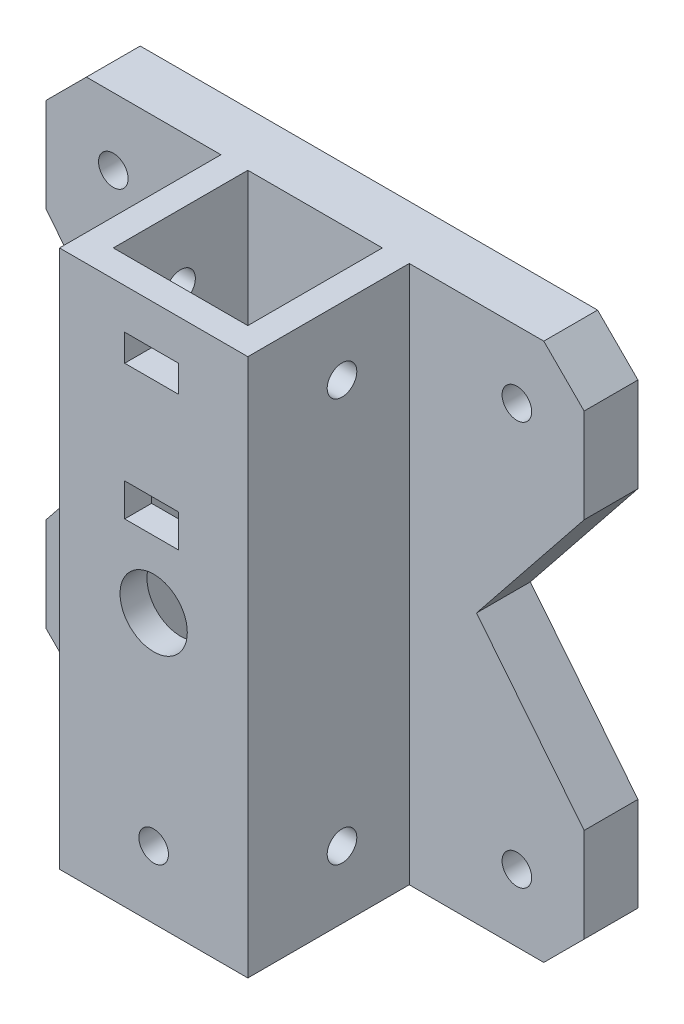
SolidWorks part; units mm, degrees
ref_plane "Plan de face" through (0, 0, 0) normal (0, 0, 1) x (1, 0, 0)
ref_plane "Plan de dessus" through (0, 0, 0) normal (0, 1, 0) x (1, 0, 0)
ref_plane "Plan de droite" through (0, 0, 0) normal (1, 0, 0) x (0, 0, -1)
sketch "Esquisse1" plane through (0, 0, 0) normal (0, 0, 1) x (1, 0, 0)
  line L1 (-40, 40) -> (40, 40)
  line L2 (-40, 40) -> (-40, -40)
  line L3 (-40, -40) -> (40, -40)
  line L4 (40, 40) -> (40, -40)
  line L5 (-40, 40) -> (40, -40) construction
  line L6 (-40, -40) -> (40, 40) construction
  point P0 (0, 0)
  dimension "D1" = 80
  dimension "D2" = 80
extrude "Boss.-Extru.1" add sketch "Esquisse1" along normal blind 8
sketch "Esquisse2" plane through (0, 40, 0) normal (0, 1, 0) x (1, 0, 0)
  line L0 (40, -8) -> (-40, -8) construction
  line L1 (-10, -8) -> (10, -8)
  line L2 (-10, -8) -> (-10, -28)
  line L3 (-10, -28) -> (10, -28)
  line L4 (10, -8) -> (10, -28)
  line L5 (0, -8) -> (0, 0) construction
  line L6 (40, 0) -> (-40, 0) construction
  line L7 (-14, -4) -> (-14, -32)
  line L8 (-14, -32) -> (14, -32)
  line L9 (14, -4) -> (14, -32)
  line L10 (-14, -4) -> (14, -4)
  dimension "D1" = 20
  dimension "D2" = 20
  dimension "D3" = 4
extrude "Boss.-Extru.2" add sketch "Esquisse2" against normal through all
hole_wizard "Dégagement M41" positions "Esquisse5" profile "Esquisse4" hole size "M4" standard "Din" end condition through all
sketch "Esquisse5" plane through (0, 0, 0) normal (0, 0, -1) x (-1, 0, 0)
  line L0 (-40, -40) -> (-40, 40) construction
  line L2 (-40, 40) -> (40, 40) construction
  line L3 (40, 40) -> (40, -40) construction
  line L4 (40, -40) -> (-40, -40) construction
  point P0 (-30, 30)
  point P2 (30, 30)
  point P4 (30, -30)
  point P6 (-30, -30)
  point P29 (0, 0)
  dimension "D1" = 10
  dimension "D2" = 10
  dimension "D3" = 10
  dimension "D4" = 10
sketch "Esquisse4" plane through (30, 30, 0) normal (1, 0, 0) x (0, 1, 0)
  line L0 (0, 0) -> (0, 32)
  line L1 (0, 32) -> (2.2, 32)
  line L2 (2.2, 32) -> (2.2, 0)
  line L5 (2.2, 0) -> (0, 0)
  line L11 (0, -6.35) -> (0, 107.95) construction
  dimension "Diamètre du perçage jusqu'au prochain" = 4.4
  dimension "Profondeur du perçage jusqu'au prochain" = 32
hole_wizard "Dégagement M42" positions "Esquisse7" profile "Esquisse8" hole size "M4" standard "Din" end condition through all
sketch "Esquisse7" plane through (14, 0, 0) normal (1, 0, 0) x (0, 0, -1)
  line L0 (-18, 40) -> (-18, -40) construction
  line L1 (-32, 40) -> (-8, 40) construction
  line L2 (-32, -40) -> (-8, -40) construction
  line L3 (-32, -40) -> (-32, 40) construction
  point P0 (-18, 30)
  point P2 (-18, -30)
  dimension "D1" = 14
  dimension "D2" = 10
  dimension "D3" = 10
sketch "Esquisse8" plane through (14, 30, 18) normal (0, 1, 0) x (0, 0, -1)
  line L0 (0, 0) -> (0, 54)
  line L1 (0, 54) -> (2.2, 54)
  line L2 (2.2, 54) -> (2.2, 0)
  line L5 (2.2, 0) -> (0, 0)
  line L11 (0, -6.35) -> (0, 107.95) construction
  dimension "Diamètre du perçage jusqu'au prochain" = 4.4
  dimension "Profondeur du perçage jusqu'au prochain" = 54
hole_wizard "Dégagement M101" positions "Esquisse10" profile "Esquisse9" hole size "M10" standard "Din"
sketch "Esquisse10" plane through (0, 0, 32) normal (0, 0, 1) x (1, 0, 0)
  point P0 (0, 0)
sketch "Esquisse9" plane through (0, 0, 32) normal (1, 0, 0) x (0, -1, 0)
  line L0 (0, 0) -> (0, 28)
  line L1 (0, 28) -> (5, 28)
  line L2 (5, 28) -> (5, 0)
  line L5 (5, 0) -> (0, 0)
  line L10 (0, 28) -> (-5, 28) construction
  line L11 (0, -6.35) -> (0, 107.95) construction
  dimension "Diamètre du perçage" = 10
  dimension "Profondeur du perçage" = 28
  dimension "Angle de pointe" = 180
hole_wizard "Dégagement M43" positions "Esquisse12" profile "Esquisse11" hole size "M4" standard "Din"
sketch "Esquisse12" plane through (0, 0, 32) normal (0, 0, 1) x (1, 0, 0)
  line L0 (0, -40) -> (0, 40) construction
  line L1 (-14, -40) -> (14, -40) construction
  line L2 (-14, 40) -> (14, 40) construction
  point P0 (0, -30)
  dimension "D1" = 10
sketch "Esquisse11" plane through (0, -30, 32) normal (1, 0, 0) x (0, -1, 0)
  line L0 (0, 0) -> (0, 5)
  line L1 (0, 5) -> (2.2, 5)
  line L2 (2.2, 5) -> (2.2, 0)
  line L5 (2.2, 0) -> (0, 0)
  line L10 (0, 5) -> (-2.2, 5) construction
  line L11 (0, -6.35) -> (0, 107.95) construction
  dimension "Diamètre du perçage" = 4.4
  dimension "Profondeur du perçage" = 5
  dimension "Angle de pointe" = 180
sketch "Esquisse13" plane through (0, 0, 32) normal (0, 0, 1) x (1, 0, 0)
  line L0 (-14, 40) -> (14, 40) construction
  line L1 (-4.3075, 34) -> (3.6925, 34)
  line L2 (-4.3075, 34) -> (-4.3075, 30)
  line L3 (-4.3075, 30) -> (3.6925, 30)
  line L4 (3.6925, 34) -> (3.6925, 30)
  line L5 (-4.3075, 14.855) -> (3.6925, 14.855)
  line L6 (-4.3075, 14.855) -> (-4.3075, 9.9565)
  line L7 (-4.3075, 9.9565) -> (3.6925, 9.9565)
  line L8 (3.6925, 14.855) -> (3.6925, 9.9565)
  dimension "D1" = 6
  dimension "D2" = 15.145
  dimension "D3" = 4.8985
  dimension "D4" = 4
  dimension "D5" = 8
extrude "Enlèv. mat.-Extru.1" cut sketch "Esquisse13" against normal blind 4
sketch "Esquisse14" plane through (0, 0, 8) normal (0, 0, 1) x (1, 0, 0)
  line L0 (-40, 20) -> (-24, 0)
  line L1 (-40, 40) -> (-40, -40) construction
  line L2 (-24, 0) -> (-40, -20)
  line L3 (-40, -20) -> (-40, 20)
  line L4 (-40, 0) -> (0, 0) construction
  line L5 (0, 0) -> (0, 40) construction
  line L6 (-14, 40) -> (14, 40) construction
  line L7 (40, 20) -> (24, 0)
  line L8 (40, -20) -> (40, 20)
  line L9 (24, 0) -> (40, -20)
  dimension "D1" = 16
  dimension "D2" = 40
extrude "Enlèv. mat.-Extru.2" cut sketch "Esquisse14" against normal through all
chamfer "Chanfrein2" distance 6 angle 45 4 edges at (40, -40, 4) (-40, -40, 4) (40, 40, 4) (-40, 40, 4)
move or copy body "Corps-Déplacer/Copier1" [suppressed] bodies to move or copy 108
